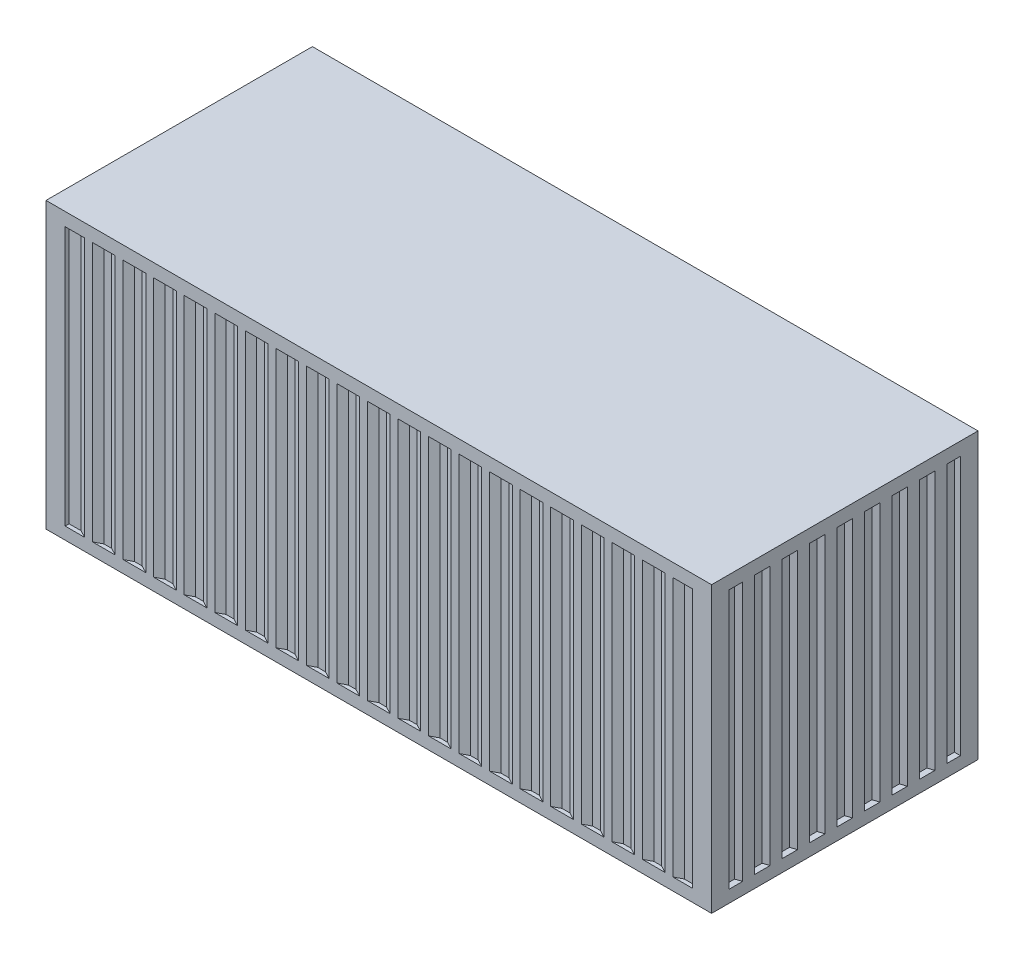
SolidWorks part; units mm, degrees
ref_plane "Front Plane" through (0, 0, 0) normal (0, 0, 1) x (1, 0, 0)
ref_plane "Top Plane" through (0, 0, 0) normal (0, 1, 0) x (1, 0, 0)
ref_plane "Right Plane" through (0, 0, 0) normal (1, 0, 0) x (0, 0, -1)
sketch "Sketch1" plane through (0, 0, 0) normal (0, 1, 0) x (1, 0, 0)
  line L1 (0, 0) -> (6058, 0)
  line L2 (0, 0) -> (0, 2424.7)
  line L3 (0, 2424.7) -> (6058, 2424.7)
  line L4 (6058, 0) -> (6058, 2424.7)
  dimension "D1" = 6058
  dimension "D2" = 2424.7
extrude "Boss-Extrude1" add sketch "Sketch1" along normal blind 2591
ref_plane "Plane-Mid-Length" through (0, 0, -1212.35) normal (0, 0, 1) x (1, 0, 0)
ref_plane "Plane-Mid-Width" through (3029, 0, 0) normal (-1, 0, 0) x (0, 0, 1)
ref_plane "Plane-Mid-Height" through (0, 1295.5, 0) normal (0, 1, 0) x (1, 0, 0)
ref_plane "Top of Corrugation" through (0, 2471, 0) normal (0, 1, 0) x (1, 0, 0)
ref_plane "Bottom of Corrugation" through (0, 111, 0) normal (0, 1, 0) x (1, 0, 0)
sketch "Sketch4" plane through (0, 2591, 0) normal (0, 1, 0) x (1, 0, 0)
  line L0 (6058, 2424.7) -> (5884, 2424.7)
  line L1 (6058, 2424.7) -> (0, 2424.7) construction
  line L2 (5884, 2424.7) -> (5884, 2388.7)
  line L3 (5884, 2388.7) -> (5774, 2388.7)
  line L4 (5774, 2388.7) -> (5706, 2424.7)
  line L5 (5706, 2424.7) -> (5634, 2424.7)
  line L6 (5634, 2424.7) -> (5566, 2388.7)
  line L7 (5566, 2388.7) -> (5496, 2388.7)
  line L8 (5496, 2388.7) -> (5428, 2424.7)
  line L9 (5428, 2424.7) -> (5356, 2424.7)
  line L10 (5356, 2424.7) -> (5288, 2388.7)
  line L11 (5288, 2388.7) -> (5218, 2388.7)
  line L12 (5218, 2388.7) -> (5150, 2424.7)
  line L13 (5150, 2424.7) -> (5078, 2424.7)
  line L14 (5078, 2424.7) -> (5010, 2388.7)
  line L15 (5010, 2388.7) -> (4940, 2388.7)
  line L16 (4940, 2388.7) -> (4872, 2424.7)
  line L17 (4872, 2424.7) -> (4800, 2424.7)
  line L18 (4800, 2424.7) -> (4732, 2388.7)
  line L19 (4732, 2388.7) -> (4662, 2388.7)
  line L20 (4662, 2388.7) -> (4594, 2424.7)
  line L21 (4594, 2424.7) -> (4522, 2424.7)
  line L22 (4522, 2424.7) -> (4454, 2388.7)
  line L23 (4454, 2388.7) -> (4384, 2388.7)
  line L24 (4384, 2388.7) -> (4316, 2424.7)
  line L25 (4316, 2424.7) -> (4244, 2424.7)
  line L26 (4244, 2424.7) -> (4176, 2388.7)
  line L27 (4176, 2388.7) -> (4106, 2388.7)
  line L28 (4106, 2388.7) -> (4038, 2424.7)
  line L29 (4038, 2424.7) -> (3966, 2424.7)
  line L30 (3966, 2424.7) -> (3898, 2388.7)
  line L31 (3898, 2388.7) -> (3828, 2388.7)
  line L32 (3828, 2388.7) -> (3760, 2424.7)
  line L33 (3760, 2424.7) -> (3688, 2424.7)
  line L34 (3688, 2424.7) -> (3620, 2388.7)
  line L35 (3620, 2388.7) -> (3550, 2388.7)
  line L36 (3550, 2388.7) -> (3482, 2424.7)
  line L37 (3482, 2424.7) -> (3410, 2424.7)
  line L38 (3410, 2424.7) -> (3342, 2388.7)
  line L39 (3342, 2388.7) -> (3272, 2388.7)
  line L40 (3272, 2388.7) -> (3204, 2424.7)
  line L41 (3204, 2424.7) -> (3132, 2424.7)
  line L42 (3132, 2424.7) -> (3064, 2388.7)
  line L43 (3064, 2388.7) -> (2994, 2388.7)
  line L44 (2994, 2388.7) -> (2926, 2424.7)
  line L45 (2926, 2424.7) -> (2854, 2424.7)
  line L46 (2854, 2424.7) -> (2786, 2388.7)
  line L47 (2786, 2388.7) -> (2716, 2388.7)
  line L48 (2716, 2388.7) -> (2648, 2424.7)
  line L49 (2648, 2424.7) -> (2576, 2424.7)
  line L50 (2576, 2424.7) -> (2508, 2388.7)
  line L51 (2508, 2388.7) -> (2438, 2388.7)
  line L52 (2438, 2388.7) -> (2370, 2424.7)
  line L53 (2370, 2424.7) -> (2298, 2424.7)
  line L54 (2298, 2424.7) -> (2230, 2388.7)
  line L55 (2230, 2388.7) -> (2160, 2388.7)
  line L56 (2160, 2388.7) -> (2092, 2424.7)
  line L57 (2092, 2424.7) -> (2020, 2424.7)
  line L58 (2020, 2424.7) -> (1952, 2388.7)
  line L59 (1952, 2388.7) -> (1882, 2388.7)
  line L60 (1882, 2388.7) -> (1814, 2424.7)
  line L61 (1814, 2424.7) -> (1742, 2424.7)
  line L62 (1742, 2424.7) -> (1674, 2388.7)
  line L63 (1674, 2388.7) -> (1604, 2388.7)
  line L64 (1604, 2388.7) -> (1536, 2424.7)
  line L65 (1536, 2424.7) -> (1464, 2424.7)
  line L66 (1464, 2424.7) -> (1396, 2388.7)
  line L67 (1396, 2388.7) -> (1326, 2388.7)
  line L68 (1326, 2388.7) -> (1258, 2424.7)
  line L69 (1258, 2424.7) -> (1186, 2424.7)
  line L70 (1186, 2424.7) -> (1118, 2388.7)
  line L71 (1118, 2388.7) -> (1048, 2388.7)
  line L72 (1048, 2388.7) -> (980, 2424.7)
  line L73 (980, 2424.7) -> (908, 2424.7)
  line L74 (908, 2424.7) -> (840, 2388.7)
  line L75 (840, 2388.7) -> (770, 2388.7)
  line L76 (770, 2388.7) -> (702, 2424.7)
  line L77 (702, 2424.7) -> (630, 2424.7)
  line L78 (630, 2424.7) -> (562, 2388.7)
  line L79 (562, 2388.7) -> (492, 2388.7)
  line L80 (492, 2388.7) -> (424, 2424.7)
  line L81 (0, 2424.7) -> (174, 2424.7)
  line L82 (174, 2424.7) -> (174, 2388.7)
  line L83 (174, 2388.7) -> (284, 2388.7)
  line L84 (284, 2388.7) -> (352, 2424.7)
  line L85 (352, 2424.7) -> (424, 2424.7)
  line L86 (-1425.05, 1212.35) -> (1425.05, 1212.35) construction
  line L87 (352, 0) -> (424, 0)
  line L88 (284, 36) -> (352, 0)
  line L89 (174, 36) -> (284, 36)
  line L90 (174, 0) -> (174, 36)
  line L91 (0, 0) -> (174, 0)
  line L92 (492, 36) -> (424, 0)
  line L93 (562, 36) -> (492, 36)
  line L94 (630, 0) -> (562, 36)
  line L95 (702, 0) -> (630, 0)
  line L96 (770, 36) -> (702, 0)
  line L97 (840, 36) -> (770, 36)
  line L98 (908, 0) -> (840, 36)
  line L99 (980, 0) -> (908, 0)
  line L100 (1048, 36) -> (980, 0)
  line L101 (1118, 36) -> (1048, 36)
  line L102 (1186, 0) -> (1118, 36)
  line L103 (1258, 0) -> (1186, 0)
  line L104 (1326, 36) -> (1258, 0)
  line L105 (1396, 36) -> (1326, 36)
  line L106 (1464, 0) -> (1396, 36)
  line L107 (1536, 0) -> (1464, 0)
  line L108 (1604, 36) -> (1536, 0)
  line L109 (1674, 36) -> (1604, 36)
  line L110 (1742, 0) -> (1674, 36)
  line L111 (1814, 0) -> (1742, 0)
  line L112 (1882, 36) -> (1814, 0)
  line L113 (1952, 36) -> (1882, 36)
  line L114 (2020, 0) -> (1952, 36)
  line L115 (2092, 0) -> (2020, 0)
  line L116 (2160, 36) -> (2092, 0)
  line L117 (2230, 36) -> (2160, 36)
  line L118 (2298, 0) -> (2230, 36)
  line L119 (2370, 0) -> (2298, 0)
  line L120 (2438, 36) -> (2370, 0)
  line L121 (2508, 36) -> (2438, 36)
  line L122 (2576, 0) -> (2508, 36)
  line L123 (2648, 0) -> (2576, 0)
  line L124 (2716, 36) -> (2648, 0)
  line L125 (2786, 36) -> (2716, 36)
  line L126 (2854, 0) -> (2786, 36)
  line L127 (2926, 0) -> (2854, 0)
  line L128 (2994, 36) -> (2926, 0)
  line L129 (3064, 36) -> (2994, 36)
  line L130 (3132, 0) -> (3064, 36)
  line L131 (3204, 0) -> (3132, 0)
  line L132 (3272, 36) -> (3204, 0)
  line L133 (3342, 36) -> (3272, 36)
  line L134 (3410, 0) -> (3342, 36)
  line L135 (3482, 0) -> (3410, 0)
  line L136 (3550, 36) -> (3482, 0)
  line L137 (3620, 36) -> (3550, 36)
  line L138 (3688, 0) -> (3620, 36)
  line L139 (3760, 0) -> (3688, 0)
  line L140 (3828, 36) -> (3760, 0)
  line L141 (3898, 36) -> (3828, 36)
  line L142 (3966, 0) -> (3898, 36)
  line L143 (4038, 0) -> (3966, 0)
  line L144 (4106, 36) -> (4038, 0)
  line L145 (4176, 36) -> (4106, 36)
  line L146 (4244, 0) -> (4176, 36)
  line L147 (4316, 0) -> (4244, 0)
  line L148 (4384, 36) -> (4316, 0)
  line L149 (4454, 36) -> (4384, 36)
  line L150 (4522, 0) -> (4454, 36)
  line L151 (4594, 0) -> (4522, 0)
  line L152 (4662, 36) -> (4594, 0)
  line L153 (4732, 36) -> (4662, 36)
  line L154 (4800, 0) -> (4732, 36)
  line L155 (4872, 0) -> (4800, 0)
  line L156 (4940, 36) -> (4872, 0)
  line L157 (5010, 36) -> (4940, 36)
  line L158 (5078, 0) -> (5010, 36)
  line L159 (5150, 0) -> (5078, 0)
  line L160 (5218, 36) -> (5150, 0)
  line L161 (5288, 36) -> (5218, 36)
  line L162 (5356, 0) -> (5288, 36)
  line L163 (5428, 0) -> (5356, 0)
  line L164 (5496, 36) -> (5428, 0)
  line L165 (5566, 36) -> (5496, 36)
  line L166 (5634, 0) -> (5566, 36)
  line L167 (5706, 0) -> (5634, 0)
  line L168 (5774, 36) -> (5706, 0)
  line L169 (5884, 36) -> (5774, 36)
  line L170 (5884, 0) -> (5884, 36)
  line L171 (6058, 0) -> (5884, 0)
  line L172 (6058, 2424.7) -> (6058, 2264.7)
  line L173 (6058, 0) -> (6058, 2424.7) construction
  line L174 (6058, 2264.7) -> (6003, 2264.7)
  line L175 (6003, 2264.7) -> (6003, 2160.35)
  line L176 (6003, 2160.35) -> (6058, 2142.35)
  line L177 (6058, 2142.35) -> (6058, 2032.35)
  line L178 (6058, 2032.35) -> (6003, 2014.35)
  line L179 (6003, 2014.35) -> (6003, 1910.35)
  line L180 (6003, 1910.35) -> (6058, 1892.35)
  line L181 (6058, 1892.35) -> (6058, 1782.35)
  line L182 (6058, 1782.35) -> (6003, 1764.35)
  line L183 (6003, 1764.35) -> (6003, 1660.35)
  line L184 (6003, 1660.35) -> (6058, 1642.35)
  line L185 (6058, 1642.35) -> (6058, 1532.35)
  line L186 (6058, 1532.35) -> (6003, 1514.35)
  line L187 (6003, 1514.35) -> (6003, 1410.35)
  line L188 (6003, 1410.35) -> (6058, 1392.35)
  line L189 (6058, 1392.35) -> (6058, 1282.35)
  line L190 (6058, 1282.35) -> (6003, 1264.35)
  line L191 (6003, 1264.35) -> (6003, 1160.35)
  line L192 (6003, 1160.35) -> (6058, 1142.35)
  line L193 (6058, 1142.35) -> (6058, 1032.35)
  line L194 (6058, 1032.35) -> (6003, 1014.35)
  line L195 (6003, 1014.35) -> (6003, 910.35)
  line L196 (6003, 910.35) -> (6058, 892.35)
  line L197 (6058, 892.35) -> (6058, 782.35)
  line L198 (6058, 782.35) -> (6003, 764.35)
  line L199 (6003, 764.35) -> (6003, 660.35)
  line L200 (6003, 660.35) -> (6058, 642.35)
  line L201 (6058, 642.35) -> (6058, 532.35)
  line L202 (6058, 532.35) -> (6003, 514.35)
  line L203 (6003, 514.35) -> (6003, 410.35)
  line L204 (6058, 0) -> (6058, 160)
  line L205 (6058, 160) -> (6003, 160)
  line L206 (6003, 160) -> (6003, 264.35)
  line L207 (6003, 264.35) -> (6058, 282.35)
  line L208 (6058, 282.35) -> (6058, 392.35)
  line L209 (6058, 392.35) -> (6003, 410.35)
  line L210 (0, 2424.7) -> (-440.0749, 2424.7)
  line L211 (-440.0749, 2424.7) -> (-440.0749, 3030.4857)
  line L212 (-440.0749, 3030.4857) -> (7385.1907, 3030.4857)
  line L213 (7385.1907, 3030.4857) -> (7385.1907, -895.4636)
  line L214 (7385.1907, -895.4636) -> (-1155.3936, -895.4636)
  line L215 (-1155.3936, -895.4636) -> (-1155.3936, 0)
  line L216 (-1155.3936, 0) -> (0, 0)
  dimension "D1" = 174
  dimension "D2" = 36
  dimension "D3" = 36
  dimension "D4" = 72
  dimension "D5" = 68
  dimension "D6" = 68
  dimension "D7" = 70
  dimension "D8" = 68
  dimension "D9" = 110
  dimension "D11" = 174
  dimension "D12" = 72
  dimension "D13" = 68
  dimension "D14" = 160
  dimension "D15" = 160
  dimension "D16" = 55
  dimension "D17" = 104.35
  dimension "D18" = 18
  dimension "D19" = 18
  dimension "D20" = 110
  dimension "D21" = 104
  dimension "D23" = 18
  dimension "D24" = 18
  dimension "D25" = 110
  dimension "D10" = 19
  dimension "D22" = 7
extrude "Cut-Extrude1" cut sketch "Sketch4" against normal up to surface (2360 mm away) from surface at -120 up to plane "Bottom of Corrugation" starting at plane "Top of Corrugation"
sketch "Sketch5" plane through (0, 1295.5, 0) normal (0, 1, 0) x (1, 0, 0)
  line L0 (0, 2423.1) -> (172.4, 2423.1)
  line L1 (0, 2424.7) -> (0, 0) construction
  line L2 (172.4, 2423.1) -> (172.4, 2387.1)
  line L3 (172.4, 2387.1) -> (284.3974, 2387.1)
  line L4 (284.3974, 2387.1) -> (352.3974, 2423.1)
  line L5 (352.3974, 2423.1) -> (423.6026, 2423.1)
  line L6 (423.6026, 2423.1) -> (491.6026, 2387.1)
  line L7 (491.6026, 2387.1) -> (562.3974, 2387.1)
  line L8 (562.3974, 2387.1) -> (630.3974, 2423.1)
  line L9 (6058, 2424.7) -> (0, 2424.7) construction
  line L10 (174, 2388.7) -> (174, 2424.7) construction
  line L11 (284, 2388.7) -> (174, 2388.7) construction
  line L12 (352, 2424.7) -> (284, 2388.7) construction
  line L13 (492, 2388.7) -> (424, 2424.7) construction
  line L14 (562, 2388.7) -> (492, 2388.7) construction
  line L15 (630, 2424.7) -> (562, 2388.7) construction
  line L16 (630.3974, 2423.1) -> (701.6026, 2423.1)
  line L17 (701.6026, 2423.1) -> (769.6026, 2387.1)
  line L18 (769.6026, 2387.1) -> (840.3974, 2387.1)
  line L19 (840.3974, 2387.1) -> (908.3974, 2423.1)
  line L20 (908.3974, 2423.1) -> (979.6026, 2423.1)
  line L21 (979.6026, 2423.1) -> (1047.6026, 2387.1)
  line L22 (1047.6026, 2387.1) -> (1118.3974, 2387.1)
  line L23 (1118.3974, 2387.1) -> (1186.3974, 2423.1)
  line L24 (1186.3974, 2423.1) -> (1257.6026, 2423.1)
  line L25 (1257.6026, 2423.1) -> (1325.6026, 2387.1)
  line L26 (1325.6026, 2387.1) -> (1396.3974, 2387.1)
  line L27 (1396.3974, 2387.1) -> (1464.3974, 2423.1)
  line L28 (1464.3974, 2423.1) -> (1535.6026, 2423.1)
  line L29 (1535.6026, 2423.1) -> (1603.6026, 2387.1)
  line L30 (1603.6026, 2387.1) -> (1674.3974, 2387.1)
  line L31 (1674.3974, 2387.1) -> (1742.3974, 2423.1)
  line L32 (1742.3974, 2423.1) -> (1813.6026, 2423.1)
  line L33 (1813.6026, 2423.1) -> (1881.6026, 2387.1)
  line L34 (1881.6026, 2387.1) -> (1952.3974, 2387.1)
  line L35 (1952.3974, 2387.1) -> (2020.3974, 2423.1)
  line L36 (2020.3974, 2423.1) -> (2091.6026, 2423.1)
  line L37 (2091.6026, 2423.1) -> (2159.6026, 2387.1)
  line L38 (2159.6026, 2387.1) -> (2230.3974, 2387.1)
  line L39 (2230.3974, 2387.1) -> (2298.3974, 2423.1)
  line L40 (2298.3974, 2423.1) -> (2369.6026, 2423.1)
  line L41 (2369.6026, 2423.1) -> (2437.6026, 2387.1)
  line L42 (2437.6026, 2387.1) -> (2508.3974, 2387.1)
  line L43 (2508.3974, 2387.1) -> (2576.3974, 2423.1)
  line L44 (2576.3974, 2423.1) -> (2647.6026, 2423.1)
  line L45 (2647.6026, 2423.1) -> (2715.6026, 2387.1)
  line L46 (2715.6026, 2387.1) -> (2786.3974, 2387.1)
  line L47 (2786.3974, 2387.1) -> (2854.3974, 2423.1)
  line L48 (2854.3974, 2423.1) -> (2925.6026, 2423.1)
  line L49 (2925.6026, 2423.1) -> (2993.6026, 2387.1)
  line L50 (2993.6026, 2387.1) -> (3064.3974, 2387.1)
  line L51 (3064.3974, 2387.1) -> (3132.3974, 2423.1)
  line L52 (3132.3974, 2423.1) -> (3203.6026, 2423.1)
  line L53 (3203.6026, 2423.1) -> (3271.6026, 2387.1)
  line L54 (3271.6026, 2387.1) -> (3342.3974, 2387.1)
  line L55 (3342.3974, 2387.1) -> (3410.3974, 2423.1)
  line L56 (3410.3974, 2423.1) -> (3481.6026, 2423.1)
  line L57 (3481.6026, 2423.1) -> (3549.6026, 2387.1)
  line L58 (3549.6026, 2387.1) -> (3620.3974, 2387.1)
  line L59 (3620.3974, 2387.1) -> (3688.3974, 2423.1)
  line L60 (3688.3974, 2423.1) -> (3759.6026, 2423.1)
  line L61 (3759.6026, 2423.1) -> (3827.6026, 2387.1)
  line L62 (3827.6026, 2387.1) -> (3898.3974, 2387.1)
  line L63 (3898.3974, 2387.1) -> (3966.3974, 2423.1)
  line L64 (3966.3974, 2423.1) -> (4037.6026, 2423.1)
  line L65 (4037.6026, 2423.1) -> (4105.6026, 2387.1)
  line L66 (4105.6026, 2387.1) -> (4176.3974, 2387.1)
  line L67 (4176.3974, 2387.1) -> (4244.3974, 2423.1)
  line L68 (4244.3974, 2423.1) -> (4315.6026, 2423.1)
  line L69 (4315.6026, 2423.1) -> (4383.6026, 2387.1)
  line L70 (4383.6026, 2387.1) -> (4454.3974, 2387.1)
  line L71 (4454.3974, 2387.1) -> (4522.3974, 2423.1)
  line L72 (4522.3974, 2423.1) -> (4593.6026, 2423.1)
  line L73 (4593.6026, 2423.1) -> (4661.6026, 2387.1)
  line L74 (4661.6026, 2387.1) -> (4732.3974, 2387.1)
  line L75 (4732.3974, 2387.1) -> (4800.3974, 2423.1)
  line L76 (4800.3974, 2423.1) -> (4871.6026, 2423.1)
  line L77 (4871.6026, 2423.1) -> (4939.6026, 2387.1)
  line L78 (4939.6026, 2387.1) -> (5010.3974, 2387.1)
  line L79 (5010.3974, 2387.1) -> (5078.3974, 2423.1)
  line L80 (5078.3974, 2423.1) -> (5149.6026, 2423.1)
  line L81 (5149.6026, 2423.1) -> (5217.6026, 2387.1)
  line L82 (5217.6026, 2387.1) -> (5288.3974, 2387.1)
  line L83 (5288.3974, 2387.1) -> (5356.3974, 2423.1)
  line L84 (5356.3974, 2423.1) -> (5427.6026, 2423.1)
  line L85 (5427.6026, 2423.1) -> (5495.6026, 2387.1)
  line L86 (5495.6026, 2387.1) -> (5566.3974, 2387.1)
  line L87 (5566.3974, 2387.1) -> (5634.3974, 2423.1)
  line L88 (5634.3974, 2423.1) -> (5705.6026, 2423.1)
  line L89 (5705.6026, 2423.1) -> (5773.6026, 2387.1)
  line L90 (5773.6026, 2387.1) -> (5885.6, 2387.1)
  line L91 (5885.6, 2387.1) -> (5885.6, 2423.1)
  line L92 (5885.6, 2423.1) -> (6056.4, 2423.1)
  line L93 (5774, 2388.7) -> (5706, 2424.7) construction
  line L94 (5884, 2388.7) -> (5774, 2388.7) construction
  line L95 (5884, 2424.7) -> (5884, 2388.7) construction
  line L96 (6058, 0) -> (6058, 2424.7) construction
  line L97 (-1425.05, 1212.35) -> (1425.05, 1212.35) construction
  line L98 (5885.6, 1.6) -> (6056.4, 1.6)
  line L99 (5885.6, 37.6) -> (5885.6, 1.6)
  line L100 (5773.6026, 37.6) -> (5885.6, 37.6)
  line L101 (5705.6026, 1.6) -> (5773.6026, 37.6)
  line L102 (5634.3974, 1.6) -> (5705.6026, 1.6)
  line L103 (5566.3974, 37.6) -> (5634.3974, 1.6)
  line L104 (5495.6026, 37.6) -> (5566.3974, 37.6)
  line L105 (5427.6026, 1.6) -> (5495.6026, 37.6)
  line L106 (5356.3974, 1.6) -> (5427.6026, 1.6)
  line L107 (5288.3974, 37.6) -> (5356.3974, 1.6)
  line L108 (5217.6026, 37.6) -> (5288.3974, 37.6)
  line L109 (5149.6026, 1.6) -> (5217.6026, 37.6)
  line L110 (5078.3974, 1.6) -> (5149.6026, 1.6)
  line L111 (5010.3974, 37.6) -> (5078.3974, 1.6)
  line L112 (4939.6026, 37.6) -> (5010.3974, 37.6)
  line L113 (4871.6026, 1.6) -> (4939.6026, 37.6)
  line L114 (4800.3974, 1.6) -> (4871.6026, 1.6)
  line L115 (4732.3974, 37.6) -> (4800.3974, 1.6)
  line L116 (4661.6026, 37.6) -> (4732.3974, 37.6)
  line L117 (4593.6026, 1.6) -> (4661.6026, 37.6)
  line L118 (4522.3974, 1.6) -> (4593.6026, 1.6)
  line L119 (4454.3974, 37.6) -> (4522.3974, 1.6)
  line L120 (4383.6026, 37.6) -> (4454.3974, 37.6)
  line L121 (4315.6026, 1.6) -> (4383.6026, 37.6)
  line L122 (4244.3974, 1.6) -> (4315.6026, 1.6)
  line L123 (4176.3974, 37.6) -> (4244.3974, 1.6)
  line L124 (4105.6026, 37.6) -> (4176.3974, 37.6)
  line L125 (4037.6026, 1.6) -> (4105.6026, 37.6)
  line L126 (3966.3974, 1.6) -> (4037.6026, 1.6)
  line L127 (3898.3974, 37.6) -> (3966.3974, 1.6)
  line L128 (3827.6026, 37.6) -> (3898.3974, 37.6)
  line L129 (3759.6026, 1.6) -> (3827.6026, 37.6)
  line L130 (3688.3974, 1.6) -> (3759.6026, 1.6)
  line L131 (3620.3974, 37.6) -> (3688.3974, 1.6)
  line L132 (3549.6026, 37.6) -> (3620.3974, 37.6)
  line L133 (3481.6026, 1.6) -> (3549.6026, 37.6)
  line L134 (3410.3974, 1.6) -> (3481.6026, 1.6)
  line L135 (3342.3974, 37.6) -> (3410.3974, 1.6)
  line L136 (3271.6026, 37.6) -> (3342.3974, 37.6)
  line L137 (3203.6026, 1.6) -> (3271.6026, 37.6)
  line L138 (3132.3974, 1.6) -> (3203.6026, 1.6)
  line L139 (3064.3974, 37.6) -> (3132.3974, 1.6)
  line L140 (2993.6026, 37.6) -> (3064.3974, 37.6)
  line L141 (2925.6026, 1.6) -> (2993.6026, 37.6)
  line L142 (2854.3974, 1.6) -> (2925.6026, 1.6)
  line L143 (2786.3974, 37.6) -> (2854.3974, 1.6)
  line L144 (2715.6026, 37.6) -> (2786.3974, 37.6)
  line L145 (2647.6026, 1.6) -> (2715.6026, 37.6)
  line L146 (2576.3974, 1.6) -> (2647.6026, 1.6)
  line L147 (2508.3974, 37.6) -> (2576.3974, 1.6)
  line L148 (2437.6026, 37.6) -> (2508.3974, 37.6)
  line L149 (2369.6026, 1.6) -> (2437.6026, 37.6)
  line L150 (2298.3974, 1.6) -> (2369.6026, 1.6)
  line L151 (2230.3974, 37.6) -> (2298.3974, 1.6)
  line L152 (2159.6026, 37.6) -> (2230.3974, 37.6)
  line L153 (2091.6026, 1.6) -> (2159.6026, 37.6)
  line L154 (2020.3974, 1.6) -> (2091.6026, 1.6)
  line L155 (1952.3974, 37.6) -> (2020.3974, 1.6)
  line L156 (1881.6026, 37.6) -> (1952.3974, 37.6)
  line L157 (1813.6026, 1.6) -> (1881.6026, 37.6)
  line L158 (1742.3974, 1.6) -> (1813.6026, 1.6)
  line L159 (1674.3974, 37.6) -> (1742.3974, 1.6)
  line L160 (1603.6026, 37.6) -> (1674.3974, 37.6)
  line L161 (1535.6026, 1.6) -> (1603.6026, 37.6)
  line L162 (1464.3974, 1.6) -> (1535.6026, 1.6)
  line L163 (1396.3974, 37.6) -> (1464.3974, 1.6)
  line L164 (1325.6026, 37.6) -> (1396.3974, 37.6)
  line L165 (1257.6026, 1.6) -> (1325.6026, 37.6)
  line L166 (1186.3974, 1.6) -> (1257.6026, 1.6)
  line L167 (1118.3974, 37.6) -> (1186.3974, 1.6)
  line L168 (1047.6026, 37.6) -> (1118.3974, 37.6)
  line L169 (979.6026, 1.6) -> (1047.6026, 37.6)
  line L170 (908.3974, 1.6) -> (979.6026, 1.6)
  line L171 (840.3974, 37.6) -> (908.3974, 1.6)
  line L172 (769.6026, 37.6) -> (840.3974, 37.6)
  line L173 (701.6026, 1.6) -> (769.6026, 37.6)
  line L174 (630.3974, 1.6) -> (701.6026, 1.6)
  line L175 (562.3974, 37.6) -> (630.3974, 1.6)
  line L176 (491.6026, 37.6) -> (562.3974, 37.6)
  line L177 (423.6026, 1.6) -> (491.6026, 37.6)
  line L178 (352.3974, 1.6) -> (423.6026, 1.6)
  line L179 (284.3974, 37.6) -> (352.3974, 1.6)
  line L180 (172.4, 37.6) -> (284.3974, 37.6)
  line L181 (172.4, 1.6) -> (172.4, 37.6)
  line L182 (0, 1.6) -> (172.4, 1.6)
  line L183 (6056.4, 2423.1) -> (6056.4, 2266.3)
  line L184 (6056.4, 2266.3) -> (6001.4, 2266.3)
  line L185 (6003, 2264.7) -> (6058, 2264.7) construction
  line L186 (6001.4, 2266.3) -> (6001.4, 2159.1901)
  line L187 (6001.4, 2159.1901) -> (6056.4, 2141.1901)
  line L188 (6056.4, 2141.1901) -> (6056.4, 2033.5099)
  line L189 (6056.4, 2033.5099) -> (6001.4, 2015.5099)
  line L190 (6001.4, 2015.5099) -> (6001.4, 1909.1901)
  line L191 (6001.4, 1909.1901) -> (6056.4, 1891.1901)
  line L192 (6058, 2142.35) -> (6003, 2160.35) construction
  line L193 (6003, 2160.35) -> (6003, 2264.7) construction
  line L194 (6003, 2014.35) -> (6058, 2032.35) construction
  line L195 (6003, 1910.35) -> (6003, 2014.35) construction
  line L196 (6058, 1892.35) -> (6003, 1910.35) construction
  line L197 (6056.4, 1891.1901) -> (6056.4, 1783.5099)
  line L198 (6056.4, 1783.5099) -> (6001.4, 1765.5099)
  line L199 (6001.4, 1765.5099) -> (6001.4, 1659.1901)
  line L200 (6001.4, 1659.1901) -> (6056.4, 1641.1901)
  line L201 (6056.4, 1641.1901) -> (6056.4, 1533.5099)
  line L202 (6056.4, 1533.5099) -> (6001.4, 1515.5099)
  line L203 (6001.4, 1515.5099) -> (6001.4, 1409.1901)
  line L204 (6001.4, 1409.1901) -> (6056.4, 1391.1901)
  line L205 (6056.4, 1391.1901) -> (6056.4, 1283.5099)
  line L206 (6056.4, 1283.5099) -> (6001.4, 1265.5099)
  line L207 (6001.4, 1265.5099) -> (6001.4, 1159.1901)
  line L208 (6001.4, 1159.1901) -> (6056.4, 1141.1901)
  line L209 (6056.4, 1141.1901) -> (6056.4, 1033.5099)
  line L210 (6056.4, 1033.5099) -> (6001.4, 1015.5099)
  line L211 (6001.4, 1015.5099) -> (6001.4, 909.1901)
  line L212 (6001.4, 909.1901) -> (6056.4, 891.1901)
  line L213 (6056.4, 891.1901) -> (6056.4, 783.5099)
  line L214 (6056.4, 783.5099) -> (6001.4, 765.5099)
  line L215 (6001.4, 765.5099) -> (6001.4, 659.1901)
  line L216 (6001.4, 659.1901) -> (6056.4, 641.1901)
  line L217 (6056.4, 641.1901) -> (6056.4, 533.5099)
  line L218 (6056.4, 533.5099) -> (6001.4, 515.5099)
  line L219 (6001.4, 515.5099) -> (6001.4, 409.1901)
  line L220 (6001.4, 409.1901) -> (6056.4, 391.1901)
  dimension "D1" = 1.6
  dimension "D2" = 1.6
  dimension "D3" = 1.6
  dimension "D4" = 1.6
  dimension "D5" = 1.6
  dimension "D6" = 1.6
  dimension "D7" = 1.6
  dimension "D8" = 1.6
  dimension "D9" = 1.6
  dimension "D10" = 19
  dimension "D11" = 1.6
  dimension "D12" = 1.6
  dimension "D13" = 1.6
  dimension "D14" = 1.6
  dimension "D15" = 1.6
  dimension "D16" = 1.6
  dimension "D17" = 1.6
  dimension "D18" = 1.6
  dimension "D19" = 1.6
  dimension "D20" = 1.6
  dimension "D21" = 1.6
  dimension "D22" = 1.6
  dimension "D23" = 7
